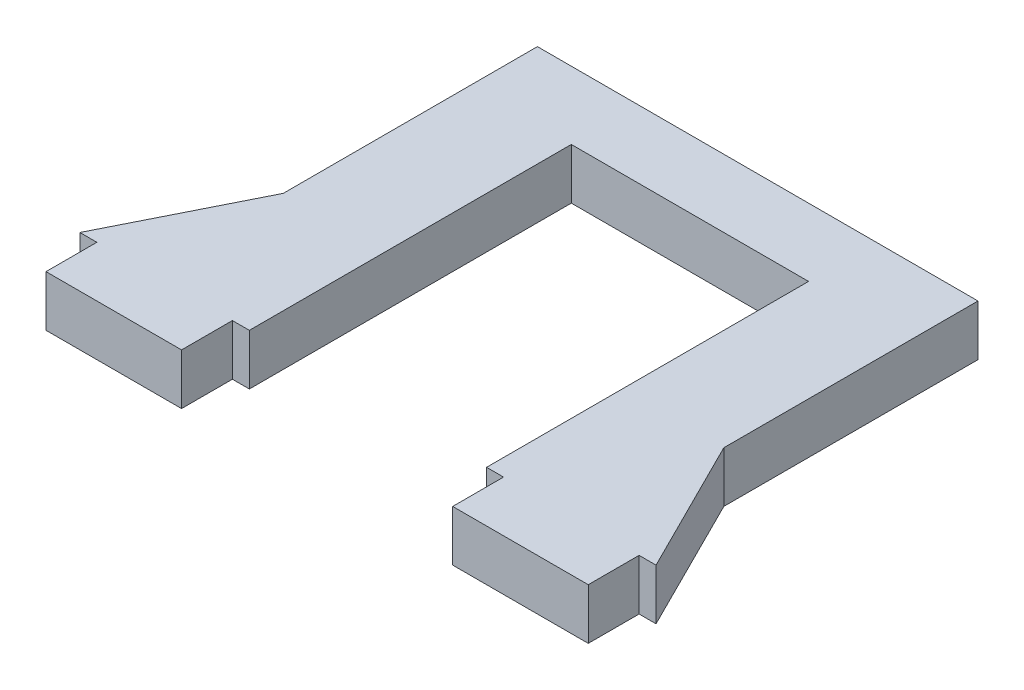
SolidWorks part; units mm, degrees
ref_plane "Plano frontal" through (0, 0, 0) normal (0, 0, 1) x (1, 0, 0)
ref_plane "Plano superior" through (0, 0, 0) normal (0, 1, 0) x (1, 0, 0)
ref_plane "Plano direito" through (0, 0, 0) normal (1, 0, 0) x (0, 0, -1)
sketch "Sketch1" plane through (0, 0, 0) normal (0, 1, 0) x (1, 0, 0)
  line L0 (7, -9.5) -> (13, -9.5)
  line L1 (-7, 9.5) -> (7, 9.5)
  line L2 (-7, 9.5) -> (-7, -9.5)
  line L4 (7, 9.5) -> (7, -9.5)
  line L5 (-13, -9.5) -> (-7, -9.5)
  line L6 (-13, -9.5) -> (-13, 13.5)
  line L7 (-13, 13.5) -> (13, 13.5)
  line L8 (13, -9.5) -> (13, 13.5)
  point P4 (-7, 0)
  point P10 (-31.9832, -14.2163)
  point P11 (0, 9.5)
  point P12 (0, 13.5)
  point P13 (-24.5278, 14)
  dimension "D1" = 19
  dimension "D2" = 4
  dimension "D3" = 14
  dimension "D4" = 6
extrude "Boss-Extrude1" add sketch "Sketch1" along normal mid plane 3
sketch "Sketch2" plane through (0, 0, 0) normal (0, 1, 0) x (1, 0, 0)
  line L0 (-13, -1.5) -> (-17, -9.5)
  line L1 (-13, 13.5) -> (-13, -9.5) construction
  line L2 (-17, -9.5) -> (-13, -9.5)
  line L3 (-13, -9.5) -> (-13, -1.5)
  line L4 (0, -1.65) -> (0, 1.65) construction
  line L5 (13, -9.5) -> (13, -1.5)
  line L6 (17, -9.5) -> (13, -9.5)
  line L7 (13, -1.5) -> (17, -9.5)
  point P4 (-15, 6.8703)
  point P7 (-24.3054, -10)
  point P13 (-15, 4.2836)
  point P14 (-15, -3.4887)
  dimension "D1" = 4
  dimension "D2" = 8
extrude "Boss-Extrude2" add sketch "Sketch2" along normal mid plane 3
sketch "Sketch3" plane through (0, 0, 0) normal (0, 1, 0) x (1, 0, 0)
  line L0 (-17, -9.5) -> (-7, -9.5) construction
  line L1 (-16, -9.5) -> (-8, -9.5)
  line L2 (-16, -9.5) -> (-16, -12.5)
  line L3 (-16, -12.5) -> (-8, -12.5)
  line L4 (-8, -9.5) -> (-8, -12.5)
  line L5 (0, -1.65) -> (0, 1.65) construction
  line L6 (8, -9.5) -> (8, -12.5)
  line L7 (16, -12.5) -> (8, -12.5)
  line L8 (16, -9.5) -> (16, -12.5)
  line L9 (16, -9.5) -> (8, -9.5)
  point P6 (-12, -9.5)
  point P7 (-12, -12.5)
  dimension "D1" = 8
  dimension "D2" = 3
  dimension "D3" = 16
extrude "Boss-Extrude3" add sketch "Sketch3" along normal mid plane 3
